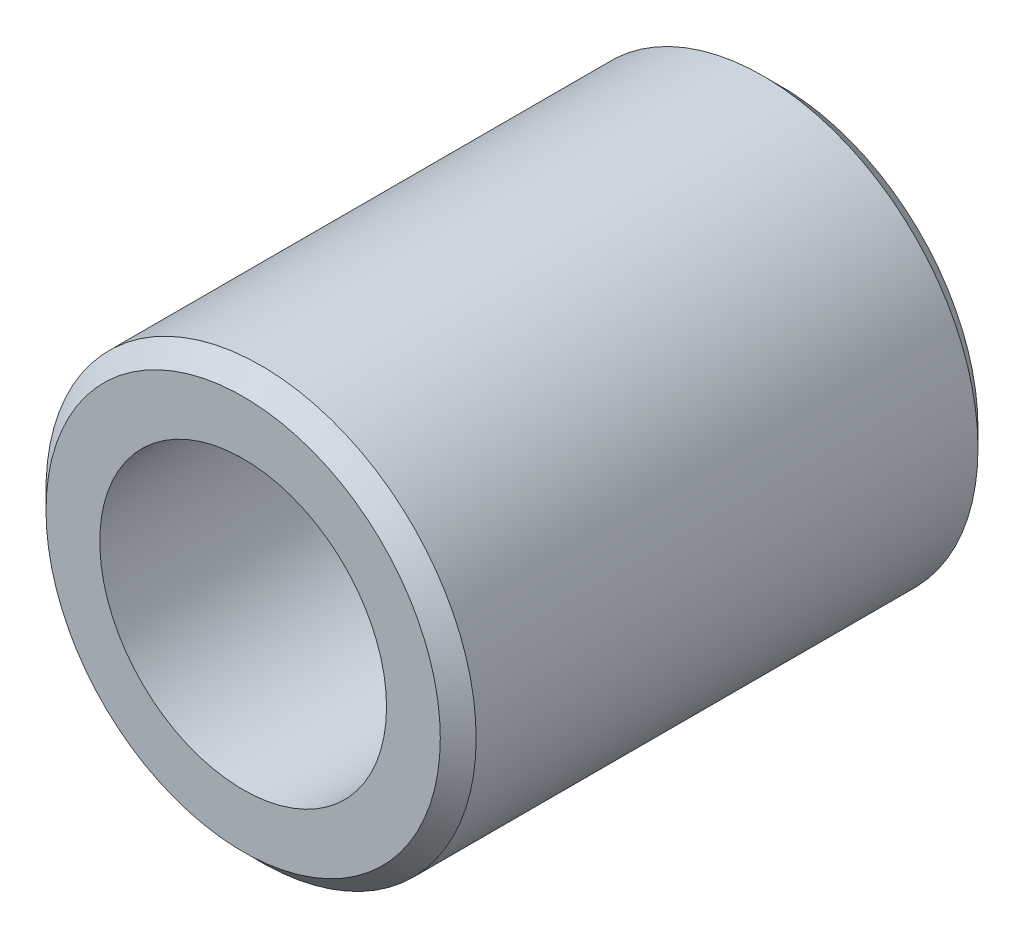
SolidWorks part; units mm, degrees
material "Brass"
ref_plane "Front Plane" through (0, 0, 0) normal (0, 0, 1) x (1, 0, 0)
ref_plane "Top Plane" through (0, 0, 0) normal (0, 1, 0) x (1, 0, 0)
ref_plane "Right Plane" through (0, 0, 0) normal (1, 0, 0) x (0, 0, -1)
sketch "Sketch1" plane through (0, 0, 0) normal (0, 0, 1) x (1, 0, 0)
  circle A0 centre (0, 0) radius 4
  dimension "D1" = 8
extrude "Extrude-Thin1" add sketch "Sketch1" along normal blind 15 thin
chamfer "Chamfer1" distance 0.5 angle 45 2 edges at (6, 0, 0) (6, 0, 15)
